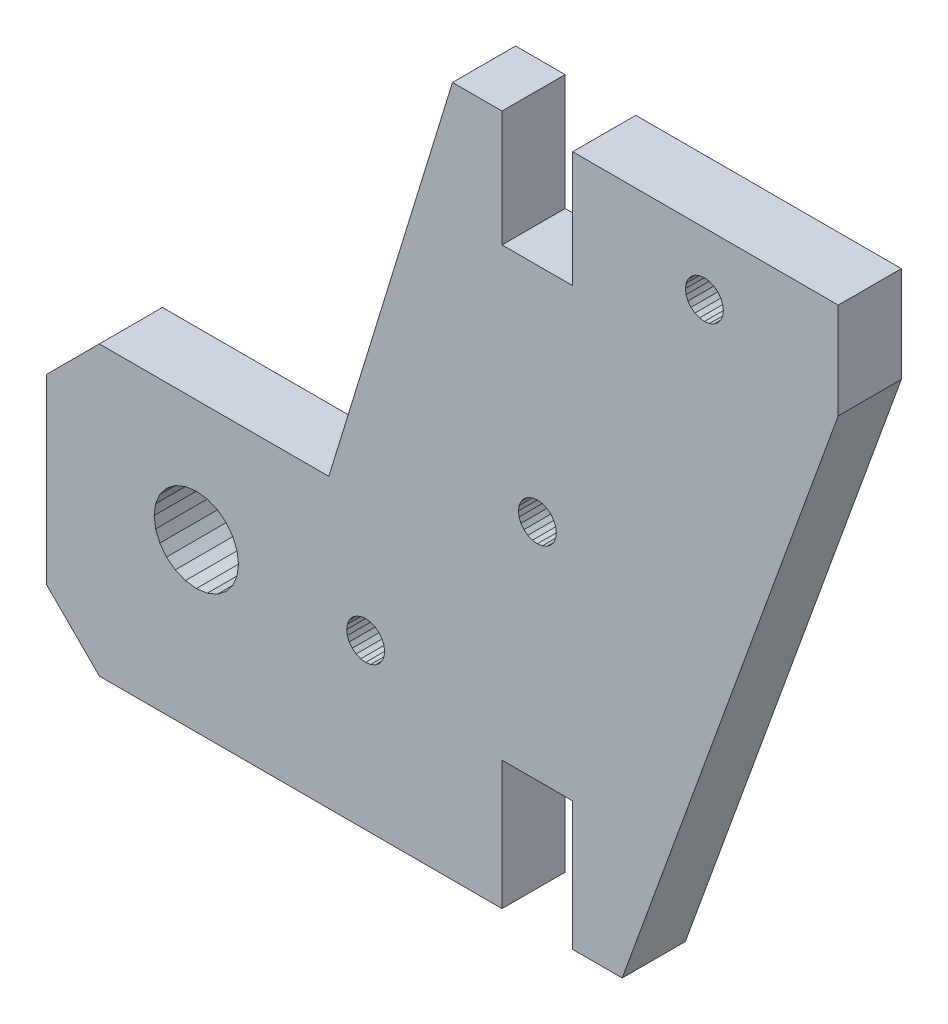
SolidWorks part; units mm, degrees
material "Maple"
ref_plane "Front Plane" through (0, 0, 0) normal (0, 0, 1) x (1, 0, 0)
ref_plane "Top Plane" through (0, 0, 0) normal (0, 1, 0) x (1, 0, 0)
ref_plane "Right Plane" through (0, 0, 0) normal (1, 0, 0) x (0, 0, -1)
sketch "Sketch1" plane through (0, 0, 0) normal (0, 0, 1) x (1, 0, 0)
  line L8233 (440.7917, 34.5416) -> (440.6115, 34.1065)
  line L8234 (442.3541, 31.8355) -> (442.821, 31.897)
  line L8235 (440.7917, 32.7375) -> (441.0784, 32.3639)
  line L8236 (441.8871, 31.897) -> (442.3541, 31.8355)
  line L8237 (441.0784, 32.3639) -> (441.452, 32.0772)
  line L8238 (441.452, 32.0772) -> (441.8871, 31.897)
  line L8239 (440.6115, 34.1065) -> (440.55, 33.6396)
  line L8240 (441.0784, 34.9152) -> (440.7917, 34.5416)
  line L8241 (455.3215, 30.266) -> (455.3215, 18.0431)
  line L8242 (441.452, 35.2019) -> (441.0784, 34.9152)
  line L8243 (442.3541, 35.4436) -> (441.8871, 35.3821)
  line L8244 (417.0355, 18.0431) -> (412.0243, 23.0543)
  line L8245 (444.0966, 34.1065) -> (443.9164, 34.5416)
  line L8246 (462.0361, 18.0431) -> (462.0361, 30.266)
  line L8247 (443.9164, 34.5416) -> (443.6297, 34.9152)
  line L8248 (440.55, 33.6396) -> (440.6115, 33.1726)
  line L8249 (442.821, 35.3821) -> (442.3541, 35.4436)
  line L8250 (444.0966, 33.1726) -> (444.1581, 33.6396)
  line L8251 (443.6297, 34.9152) -> (443.2561, 35.2019)
  line L8252 (462.0361, 30.266) -> (455.3215, 30.266)
  line L8253 (444.1581, 33.6396) -> (444.0966, 34.1065)
  line L8254 (455.3215, 18.0431) -> (417.0355, 18.0431)
  line L8255 (412.0243, 40.3886) -> (412.0243, 23.0543)
  line L8256 (438.8537, 45.3999) -> (417.0355, 45.3999)
  line L8257 (438.8537, 45.3999) -> (450.6107, 83.7146)
  line L8258 (455.3215, 83.7146) -> (455.3215, 72.6922)
  line L8259 (455.3215, 72.6922) -> (462.0361, 72.6922)
  line L8260 (462.0361, 72.6922) -> (462.0361, 83.7214)
  line L8261 (462.0361, 83.7214) -> (487.2872, 83.7214)
  line L8262 (487.2872, 83.7214) -> (487.2872, 74.6009)
  line L8263 (487.2872, 74.6009) -> (466.7469, 18.0431)
  line L8264 (412.0243, 40.3886) -> (417.0355, 45.3999)
  line L8265 (450.6107, 83.7146) -> (455.3215, 83.7146)
  line L8266 (443.2561, 32.0772) -> (443.6297, 32.3639)
  line L8267 (442.821, 31.897) -> (443.2561, 32.0772)
  line L8268 (443.6297, 32.3639) -> (443.9164, 32.7375)
  line L8269 (440.6115, 33.1726) -> (440.7917, 32.7375)
  line L8270 (443.9164, 32.7375) -> (444.0966, 33.1726)
  line L8271 (466.7469, 18.0431) -> (462.0361, 18.0431)
  line L8272 (441.8871, 35.3821) -> (441.452, 35.2019)
  line L8273 (443.2561, 35.2019) -> (442.821, 35.3821)
  line L8274 (422.3838, 34.9116) -> (422.2472, 33.874)
  line L8275 (425.2185, 37.7464) -> (424.2516, 37.3459)
  line L8276 (423.4214, 31.0393) -> (424.2516, 30.4022)
  line L8277 (423.4214, 36.7088) -> (422.7843, 35.8785)
  line L8278 (460.4828, 51.566) -> (460.4214, 52.0329)
  line L8279 (460.4214, 52.0329) -> (460.2411, 52.468)
  line L8280 (459.5808, 53.1283) -> (459.1457, 53.3085)
  line L8281 (456.9362, 51.099) -> (457.1164, 50.6639)
  line L8282 (458.6788, 53.37) -> (458.2119, 53.3085)
  line L8283 (476.1211, 76.9061) -> (475.8344, 76.5325)
  line L8284 (472.9964, 78.7101) -> (473.2831, 79.0838)
  line L8285 (473.2831, 76.5325) -> (472.9964, 76.9061)
  line L8286 (474.0918, 79.5507) -> (474.5587, 79.6122)
  line L8287 (475.0256, 76.0655) -> (474.5587, 76.0041)
  line L8288 (475.8344, 76.5325) -> (475.4607, 76.2458)
  line L8289 (430.1285, 34.9116) -> (429.728, 35.8785)
  line L8290 (474.5587, 76.0041) -> (474.0918, 76.0655)
  line L8291 (476.3628, 77.8081) -> (476.3013, 77.3412)
  line L8292 (472.8162, 78.275) -> (472.9964, 78.7101)
  line L8293 (475.4607, 79.3705) -> (475.8344, 79.0838)
  line L8294 (429.728, 35.8785) -> (429.0909, 36.7088)
  line L8295 (457.7768, 50.0036) -> (458.2119, 49.8234)
  line L8296 (474.0918, 76.0655) -> (473.6567, 76.2458)
  line L8297 (422.7843, 35.8785) -> (422.3838, 34.9116)
  line L8298 (424.2516, 37.3459) -> (423.4214, 36.7088)
  line L8299 (426.2561, 37.883) -> (425.2185, 37.7464)
  line L8300 (427.2937, 37.7464) -> (426.2561, 37.883)
  line L8301 (428.2606, 37.3459) -> (427.2937, 37.7464)
  line L8302 (429.0909, 36.7088) -> (428.2606, 37.3459)
  line L8303 (430.2651, 33.874) -> (430.1285, 34.9116)
  line L8304 (430.1285, 32.8364) -> (430.2651, 33.874)
  line L8305 (429.728, 31.8696) -> (430.1285, 32.8364)
  line L8306 (429.0909, 31.0393) -> (429.728, 31.8696)
  line L8307 (428.2606, 30.4022) -> (429.0909, 31.0393)
  line L8308 (427.2937, 30.0017) -> (428.2606, 30.4022)
  line L8309 (426.2561, 29.8651) -> (427.2937, 30.0017)
  line L8310 (425.2185, 30.0017) -> (426.2561, 29.8651)
  line L8311 (424.2516, 30.4022) -> (425.2185, 30.0017)
  line L8312 (422.7843, 31.8696) -> (423.4214, 31.0393)
  line L8313 (422.3838, 32.8364) -> (422.7843, 31.8696)
  line L8314 (422.2472, 33.874) -> (422.3838, 32.8364)
  line L8315 (460.4214, 51.099) -> (460.4828, 51.566)
  line L8316 (460.2411, 50.6639) -> (460.4214, 51.099)
  line L8317 (459.9544, 50.2903) -> (460.2411, 50.6639)
  line L8318 (459.5808, 50.0036) -> (459.9544, 50.2903)
  line L8319 (459.1457, 49.8234) -> (459.5808, 50.0036)
  line L8320 (458.6788, 49.7619) -> (459.1457, 49.8234)
  line L8321 (458.2119, 49.8234) -> (458.6788, 49.7619)
  line L8322 (457.4031, 50.2903) -> (457.7768, 50.0036)
  line L8323 (457.1164, 50.6639) -> (457.4031, 50.2903)
  line L8324 (456.8747, 51.566) -> (456.9362, 51.099)
  line L8325 (456.9362, 52.0329) -> (456.8747, 51.566)
  line L8326 (457.1164, 52.468) -> (456.9362, 52.0329)
  line L8327 (457.4031, 52.8416) -> (457.1164, 52.468)
  line L8328 (457.7768, 53.1283) -> (457.4031, 52.8416)
  line L8329 (458.2119, 53.3085) -> (457.7768, 53.1283)
  line L8330 (459.1457, 53.3085) -> (458.6788, 53.37)
  line L8331 (459.9544, 52.8416) -> (459.5808, 53.1283)
  line L8332 (460.2411, 52.468) -> (459.9544, 52.8416)
  line L8333 (475.4607, 76.2458) -> (475.0256, 76.0655)
  line L8334 (473.6567, 76.2458) -> (473.2831, 76.5325)
  line L8335 (472.9964, 76.9061) -> (472.8162, 77.3412)
  line L8336 (472.8162, 77.3412) -> (472.7547, 77.8081)
  line L8337 (472.7547, 77.8081) -> (472.8162, 78.275)
  line L8338 (473.2831, 79.0838) -> (473.6567, 79.3705)
  line L8339 (473.6567, 79.3705) -> (474.0918, 79.5507)
  line L8340 (474.5587, 79.6122) -> (475.0256, 79.5507)
  line L8341 (475.0256, 79.5507) -> (475.4607, 79.3705)
  line L8342 (475.8344, 79.0838) -> (476.1211, 78.7101)
  line L8343 (476.1211, 78.7101) -> (476.3013, 78.275)
  line L8344 (476.3013, 78.275) -> (476.3628, 77.8081)
  line L8345 (476.3013, 77.3412) -> (476.1211, 76.9061)
  line L9783 (460.7106, 63.5476) -> (456.3966, 63.5476)
  line L9784 (460.7106, 64.5476) -> (460.7106, 63.5476)
  line L9785 (460.7106, 63.5476) -> (460.7106, 62.5476)
  line L9786 (456.3966, 63.5476) -> (456.3966, 64.5476)
  line L9787 (456.3966, 63.5476) -> (456.3966, 62.5476)
extrude "Boss-Extrude1" add sketch "Sketch1" along normal blind 6
